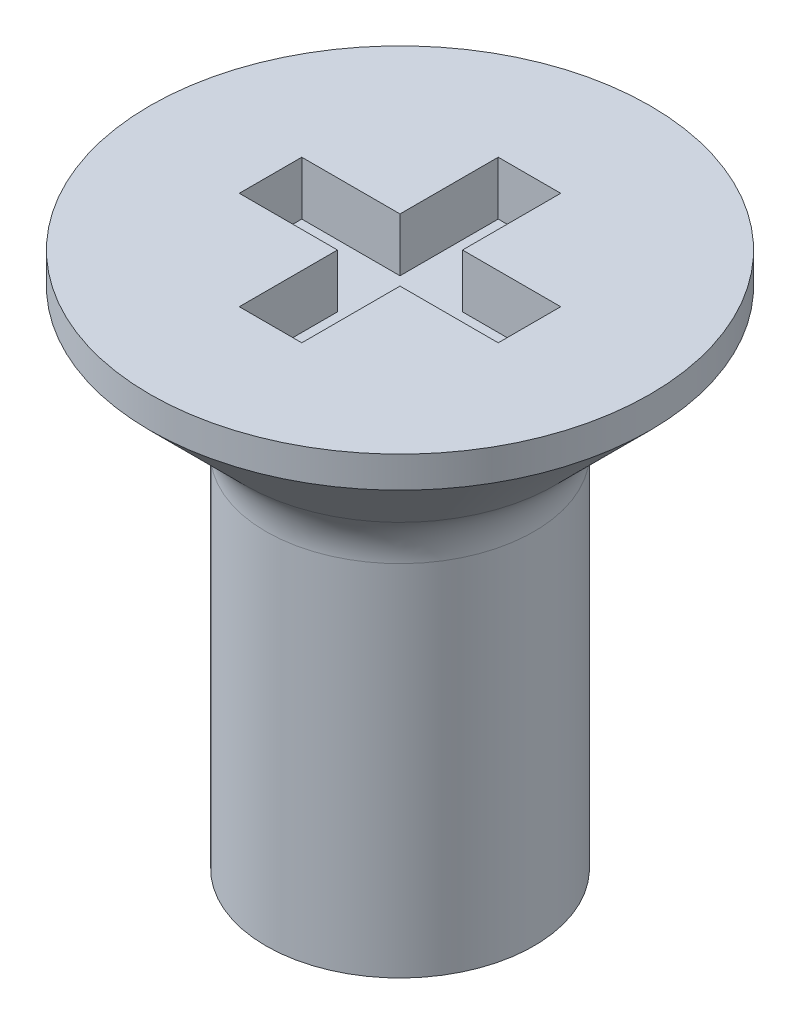
SolidWorks part; units mm, degrees
ref_plane "Front Plane" through (0, 0, 0) normal (0, 0, 1) x (1, 0, 0)
ref_plane "Top Plane" through (0, 0, 0) normal (0, 1, 0) x (1, 0, 0)
ref_plane "Right Plane" through (0, 0, 0) normal (1, 0, 0) x (0, 0, -1)
sketch "Sketch1" plane through (0, 0, 0) normal (0, 0, 1) x (1, 0, 0)
  line L0 (0, 0) -> (0, 6)
  line L1 (0, 6) -> (2.8, 6)
  line L2 (2.8, 6) -> (2.8, 5.65)
  line L3 (2.8, 5.65) -> (1.5, 4.35)
  line L4 (1.5, 4.35) -> (1.5, 0)
  line L5 (1.5, 0) -> (0, 0)
  dimension "D1" = 135
  dimension "D2" = 6
  dimension "D3" = 1.5
  dimension "D4" = 2.8
  dimension "D5" = 1.65
revolve "Revolve1" add sketch "Sketch1" angle 360 about L0
fillet "Fillet1" radius 0.8 1 edges at (0, 4.35, -1.5)
sketch "Sketch2" plane through (0, 6, 0) normal (0, 1, 0) x (1, 0, 0)
  line L1 (0.35, -1.45) -> (-0.35, -1.45)
  line L2 (0.35, -1.45) -> (0.35, 1.45)
  line L3 (0.35, 1.45) -> (-0.35, 1.45)
  line L4 (-0.35, -1.45) -> (-0.35, 1.45)
  line L5 (0.35, -1.45) -> (-0.35, 1.45) construction
  line L6 (0.35, 1.45) -> (-0.35, -1.45) construction
  line L7 (1.45, -0.35) -> (-1.45, -0.35)
  line L8 (1.45, -0.35) -> (1.45, 0.35)
  line L9 (1.45, 0.35) -> (-1.45, 0.35)
  line L10 (-1.45, -0.35) -> (-1.45, 0.35)
  line L11 (1.45, -0.35) -> (-1.45, 0.35) construction
  line L12 (1.45, 0.35) -> (-1.45, -0.35) construction
  point P0 (0, 0)
  point P6 (0, 0)
  dimension "D1" = 2.9
  dimension "D2" = 2.9
  dimension "D3" = 0.7
  dimension "D4" = 0.7
extrude "Cut-Extrude1" cut sketch "Sketch2" against normal blind 0.6 contours L10 L7 L4 L9 | L9 L2 L3 L4 | L2 L9 L4 L7 | L8 L9 L2 L7 | L2 L7 L4 L1
